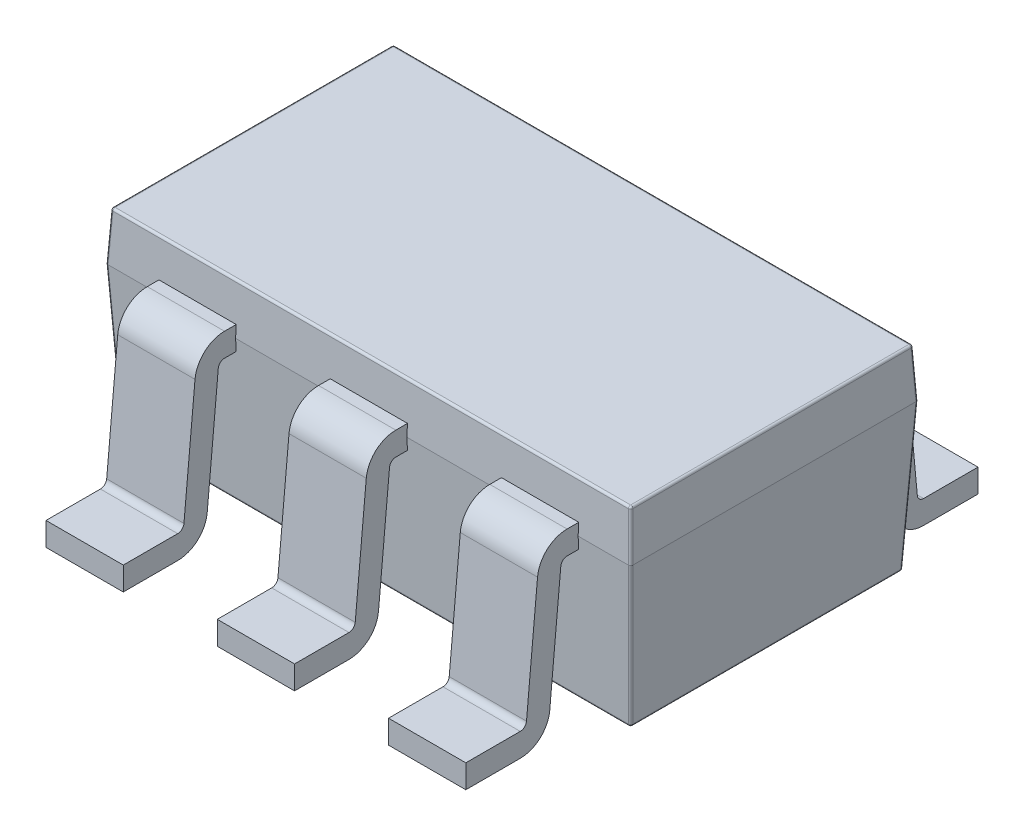
SolidWorks part; units mm, degrees
ref_plane "Front Plane" through (0, 0, 0) normal (0, 0, 1) x (1, 0, 0)
ref_plane "Top Plane" through (0, 0, 0) normal (0, 1, 0) x (1, 0, 0)
ref_plane "Right Plane" through (0, 0, 0) normal (1, 0, 0) x (0, 0, -1)
sketch "Sketch1" plane through (0, 0, 0) normal (0, 1, 0) x (1, 0, 0)
  line L0 (0, 0.9317) -> (0, -0.9273) construction
  line L1 (-1.6279, 0) -> (1.65, 0) construction
  line L3 (-1.46, 0.8) -> (1.46, 0.8)
  line L4 (-1.46, 0.8) -> (-1.46, -0.8)
  line L5 (-1.46, -0.8) -> (1.46, -0.8)
  line L6 (1.46, 0.8) -> (1.46, -0.8)
  dimension "D1" = 2.92
  dimension "D2" = 1.6
extrude "Extrude1" add sketch "Sketch1" along normal blind 0.27 draft 3 and the other way blind 0.82 draft 3
fillet "Fillet1" radius 0.0125 16 edges at (1.417, -0.82, 0) (-1.4529, 0.135, -0.7929) (0, -0.82, -0.757) (-1.4529, 0.135, 0.7929) (1.4529, 0.135, 0.7929) (1.4529, 0.135, -0.7929) (-1.4458, 0.27, 0) (0, 0.27, 0.7858) (1.4458, 0.27, 0) (0, 0.27, -0.7858) (-1.417, -0.82, 0) (0, -0.82, 0.757) (-1.4385, -0.41, -0.7785) (1.4385, -0.41, -0.7785) (1.4385, -0.41, 0.7785) (-1.4385, -0.41, 0.7785)
ref_plane "Plane1" through (0.953, 0, 0) normal (1, 0, 0) x (0, 0, -1)
sketch "Sketch3" plane through (0.953, 0, 0) normal (1, 0, 0) x (0, 0, -1)
  line L0 (-1.3536, -0.845) -> (1.2261, -0.845) construction
  line L1 (-0.757, -0.82) -> (0.757, -0.82) construction
  line L2 (-0.75, 0) -> (-0.8616, 0)
  line L3 (-0.7875, 0) -> (0.7875, 0) construction
  line L4 (-0.9611, -0.0908) -> (-1.0227, -0.7542)
  line L5 (-1.1222, -0.845) -> (-1.425, -0.845)
  arc A0 (-0.9611, -0.0908) -> (-0.8616, 0) centre (-0.8616, -0.1) cw
  arc A1 (-1.1222, -0.845) -> (-1.0227, -0.7542) centre (-1.1222, -0.745) ccw
  point P15 (-1.0311, -0.845)
  dimension "D4" = 0.1
  dimension "D1" = 0.025
  dimension "D2" = 1.425
  dimension "D3" = 0.75
  dimension "D5" = 0.1116
  dimension "D6" = 0.0615
ref_plane "Plane2" through (0, 0, 1.425) normal (0, 0, 1) x (1, 0, 0)
sketch "Sketch4" plane through (0, 0, 1.425) normal (0, 0, 1) x (1, 0, 0)
  line L0 (0.953, -1.2491) -> (0.953, -0.4409) construction
  line L1 (0.6938, -0.845) -> (1.2122, -0.845) construction
  line L3 (0.738, -0.78) -> (1.168, -0.78)
  line L4 (0.738, -0.78) -> (0.738, -0.91)
  line L5 (0.738, -0.91) -> (1.168, -0.91)
  line L6 (1.168, -0.78) -> (1.168, -0.91)
  dimension "D2" = 0.13
  dimension "D3" = 0.43
sweep "Sweep2" add profiles "Sketch4" path "Sketch3"
mirror "Espelhar2" about plane through (0, 0, 0) normal (0, 0, 1) of "Sweep2"
pattern_linear "Padrão linear1" count 3 spacing 0.953 along (-1, 0, 0) of "Sweep2"
pattern_linear "Padrão linear2" count 2 spacing 1.906 along (-1, 0, 0) of "Espelhar2"
